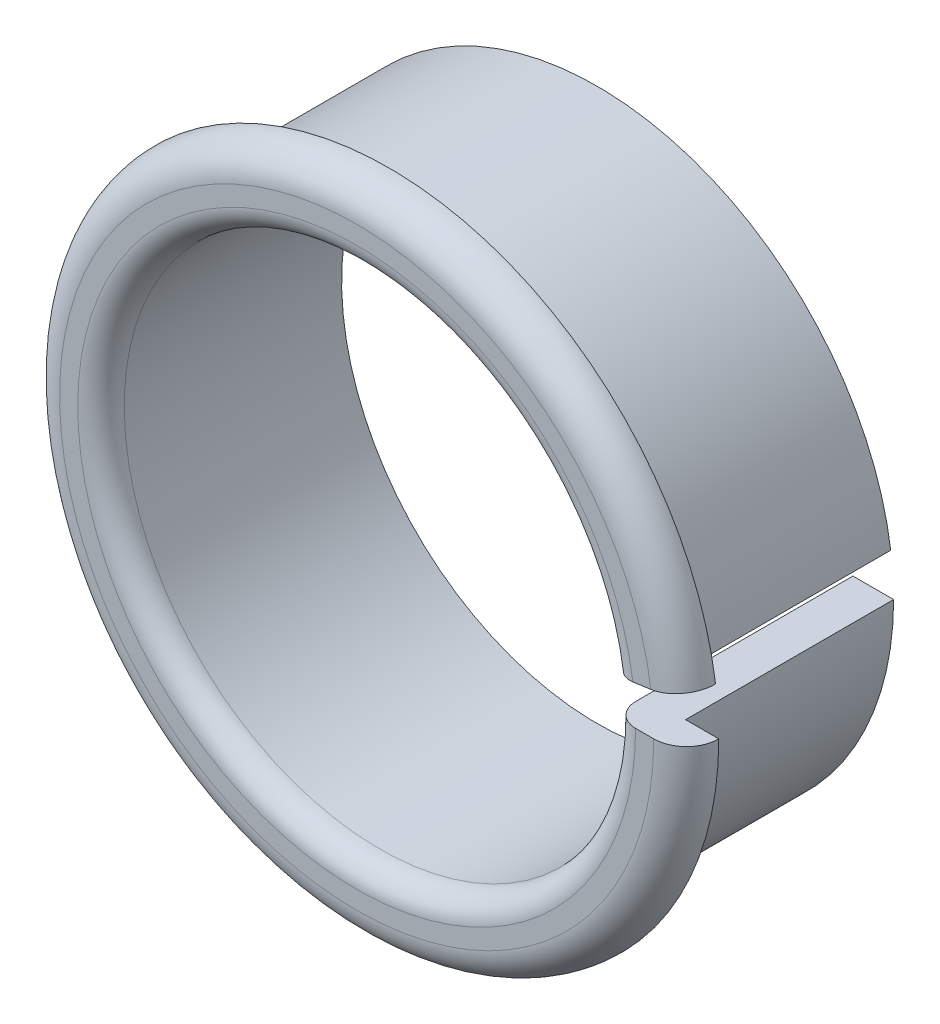
SolidWorks part; units mm, degrees
ref_plane "Front Plane" through (0, 0, 0) normal (0, 0, 1) x (1, 0, 0)
ref_plane "Top Plane" through (0, 0, 0) normal (0, 1, 0) x (1, 0, 0)
ref_plane "Right Plane" through (0, 0, 0) normal (1, 0, 0) x (0, 0, -1)
sketch "Sketch1" plane through (0, 0, 0) normal (0, 1, 0) x (1, 0, 0)
  line L0 (11, 10.35) -> (11, 1)
  line L1 (12, 0) -> (12.7822, 0)
  line L2 (11, 10.35) -> (12.75, 10.35)
  line L3 (12.75, 10.35) -> (12.75, 1.3978)
  line L4 (12.75, 1.3978) -> (14.18, 1.3978)
  arc A0 (12.7822, 0) -> (14.18, 1.3978) centre (12.7822, 1.3978) ccw
  arc A1 (11, 1) -> (12, 0) centre (12, 1) ccw
  dimension "D4" = 11
  dimension "D5" = 1
  dimension "D1" = 10.35
  dimension "D2" = 3.18
  dimension "D3" = 1.75
sketch "Sketch2" plane through (0, 0, 0) normal (0, 1, 0) x (1, 0, 0)
  line L0 (0, 0) -> (0, 15.4396) construction
revolve "Revolve1" add sketch "Sketch1" angle 352 about L0
